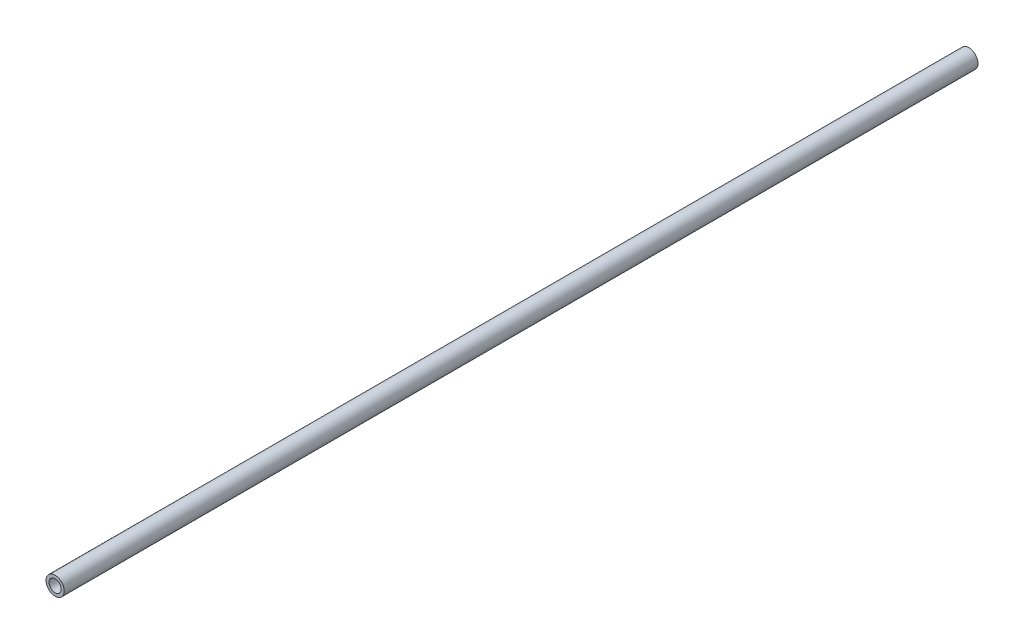
SolidWorks part; units mm, degrees
ref_plane "Front Plane" through (0, 0, 0) normal (0, 0, 1) x (1, 0, 0)
ref_plane "Top Plane" through (0, 0, 0) normal (0, 1, 0) x (1, 0, 0)
ref_plane "Right Plane" through (0, 0, 0) normal (1, 0, 0) x (0, 0, -1)
sketch "Sketch2" plane through (0, 0, 0) normal (0, 0, 1) x (1, 0, 0)
  circle A0 centre (0, 0) radius 3
  circle A1 centre (0, 0) radius 2
  dimension "D1" = 6
extrude "Boss-Extrude1" add sketch "Sketch2" along normal blind 300
